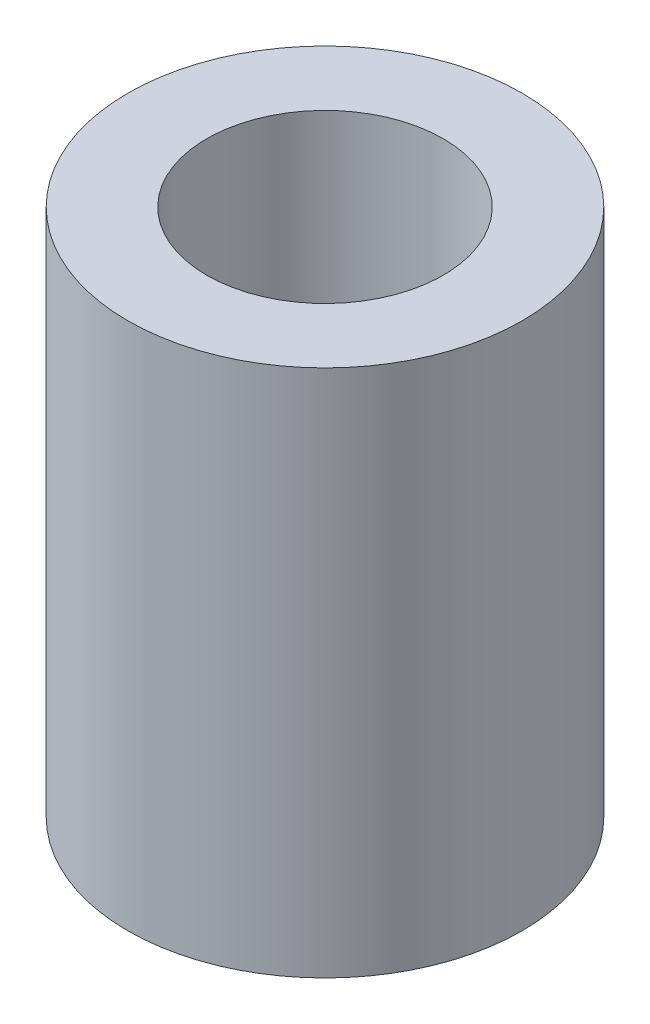
SolidWorks part; units mm, degrees
ref_plane "Front Plane" through (0, 0, 0) normal (0, 0, 1) x (1, 0, 0)
ref_plane "Top Plane" through (0, 0, 0) normal (0, 1, 0) x (1, 0, 0)
ref_plane "Right Plane" through (0, 0, 0) normal (1, 0, 0) x (0, 0, -1)
sketch "Sketch1" plane through (0, 0, 0) normal (0, 1, 0) x (1, 0, 0)
  circle A0 centre (0, 0) radius 1.5
  circle A1 centre (0, 0) radius 2.5
  dimension "D1" = 3
  dimension "D2" = 1
extrude "Boss-Extrude1" add sketch "Sketch1" along normal blind 6.7
